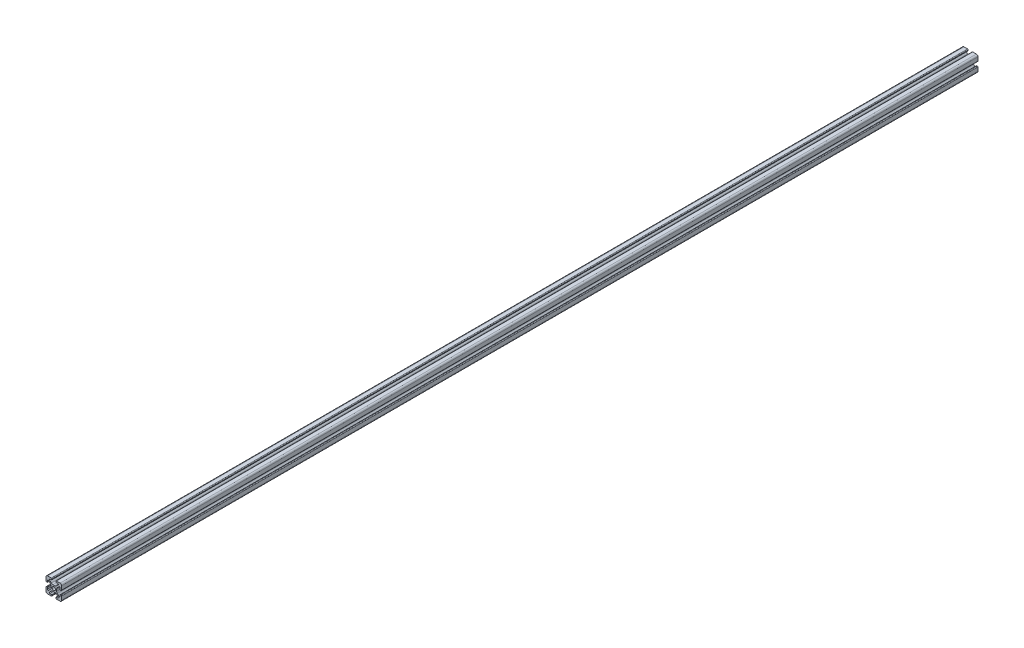
SolidWorks part; units mm, degrees
ref_plane "Front Plane" through (0, 0, 0) normal (0, 0, 1) x (1, 0, 0)
ref_plane "Top Plane" through (0, 0, 0) normal (0, 1, 0) x (1, 0, 0)
ref_plane "Right Plane" through (0, 0, 0) normal (1, 0, 0) x (0, 0, -1)
sketch "Sketch1" plane through (0, 0, 0) normal (0, 0, 1) x (1, 0, 0)
  line L2 (-9.9949, 7.9883) -> (-9.9949, 3.2893)
  line L3 (-7.9883, 9.9949) -> (-3.2893, 9.9949)
  line L4 (-2.5019, 9.2075) -> (-2.5019, 8.4963)
  line L5 (-2.8067, 8.1915) -> (-4.9149, 8.1915)
  line L6 (-5.5076, 6.7606) -> (-3.2528, 4.5058)
  line L7 (-6.7606, 5.5076) -> (-4.5058, 3.2528)
  line L8 (-8.1915, 4.9149) -> (-8.1915, 2.8067)
  line L9 (-8.4963, 2.5019) -> (-9.2075, 2.5019)
  line L11 (-1.1334, 3.6279) -> (1.1334, 3.6279)
  line L12 (-3.6279, 1.1334) -> (-3.6279, -1.1334)
  line L13 (8.4963, 2.5019) -> (9.2075, 2.5019)
  line L14 (8.1915, 4.9149) -> (8.1915, 2.8067)
  line L15 (9.9949, 7.9883) -> (9.9949, 3.2893)
  line L16 (7.9883, 9.9949) -> (3.2893, 9.9949)
  line L17 (2.5019, 9.2075) -> (2.5019, 8.4963)
  line L18 (2.8067, 8.1915) -> (4.9149, 8.1915)
  line L19 (3.6279, 1.1334) -> (3.6279, -1.1334)
  line L20 (5.5076, 6.7606) -> (3.2528, 4.5058)
  line L21 (6.7606, 5.5076) -> (4.5058, 3.2528)
  line L22 (-8.4963, -2.5019) -> (-9.2075, -2.5019)
  line L23 (-8.1915, -4.9149) -> (-8.1915, -2.8067)
  line L24 (-6.7606, -5.5076) -> (-4.5058, -3.2528)
  line L25 (-5.5076, -6.7606) -> (-3.2528, -4.5058)
  line L26 (-2.8067, -8.1915) -> (-4.9149, -8.1915)
  line L27 (-2.5019, -9.2075) -> (-2.5019, -8.4963)
  line L28 (-7.9883, -9.9949) -> (-3.2893, -9.9949)
  line L29 (-9.9949, -7.9883) -> (-9.9949, -3.2893)
  line L30 (9.9949, -7.9883) -> (9.9949, -3.2893)
  line L31 (7.9883, -9.9949) -> (3.2893, -9.9949)
  line L32 (2.5019, -9.2075) -> (2.5019, -8.4963)
  line L33 (2.8067, -8.1915) -> (4.9149, -8.1915)
  line L34 (5.5076, -6.7606) -> (3.2528, -4.5058)
  line L35 (6.7606, -5.5076) -> (4.5058, -3.2528)
  line L36 (8.1915, -4.9149) -> (8.1915, -2.8067)
  line L37 (8.4963, -2.5019) -> (9.2075, -2.5019)
  line L38 (-1.1334, -3.6279) -> (1.1334, -3.6279)
  circle A0 centre (0, 0) radius 2.1463
  arc A1 (-9.9949, 7.9883) -> (-7.9883, 9.9949) centre (-7.9883, 7.9883) cw
  arc A2 (-6.7606, 5.5076) -> (-8.1915, 4.9149) centre (-7.3533, 4.9149) ccw
  arc A3 (-4.9149, 8.1915) -> (-5.5076, 6.7606) centre (-4.9149, 7.3533) ccw
  arc A4 (-3.2893, 9.9949) -> (-2.5019, 9.2075) centre (-3.2893, 9.2075) cw
  arc A5 (-9.9949, 3.2893) -> (-9.2075, 2.5019) centre (-9.2075, 3.2893) ccw
  arc A6 (-8.1915, 2.8067) -> (-8.4963, 2.5019) centre (-8.4963, 2.8067) cw
  arc A7 (-2.5019, 8.4963) -> (-2.8067, 8.1915) centre (-2.8067, 8.4963) cw
  arc A8 (-1.1334, 3.6279) -> (-3.2528, 4.5058) centre (-1.1334, 6.6251) cw
  arc A9 (-3.6279, 1.1334) -> (-4.5058, 3.2528) centre (-6.6251, 1.1334) ccw
  arc A10 (8.1915, 2.8067) -> (8.4963, 2.5019) centre (8.4963, 2.8067) ccw
  arc A11 (9.9949, 3.2893) -> (9.2075, 2.5019) centre (9.2075, 3.2893) cw
  arc A12 (9.9949, 7.9883) -> (7.9883, 9.9949) centre (7.9883, 7.9883) ccw
  arc A13 (3.2893, 9.9949) -> (2.5019, 9.2075) centre (3.2893, 9.2075) ccw
  arc A14 (2.5019, 8.4963) -> (2.8067, 8.1915) centre (2.8067, 8.4963) ccw
  arc A15 (1.1334, 3.6279) -> (3.2528, 4.5058) centre (1.1334, 6.6251) ccw
  arc A16 (3.6279, 1.1334) -> (4.5058, 3.2528) centre (6.6251, 1.1334) cw
  arc A17 (6.7606, 5.5076) -> (8.1915, 4.9149) centre (7.3533, 4.9149) cw
  arc A18 (4.9149, 8.1915) -> (5.5076, 6.7606) centre (4.9149, 7.3533) cw
  arc A19 (-3.6279, -1.1334) -> (-4.5058, -3.2528) centre (-6.6251, -1.1334) cw
  arc A20 (-1.1334, -3.6279) -> (-3.2528, -4.5058) centre (-1.1334, -6.6251) ccw
  arc A21 (-2.5019, -8.4963) -> (-2.8067, -8.1915) centre (-2.8067, -8.4963) ccw
  arc A22 (-8.1915, -2.8067) -> (-8.4963, -2.5019) centre (-8.4963, -2.8067) ccw
  arc A23 (-9.9949, -3.2893) -> (-9.2075, -2.5019) centre (-9.2075, -3.2893) cw
  arc A24 (-3.2893, -9.9949) -> (-2.5019, -9.2075) centre (-3.2893, -9.2075) ccw
  arc A25 (-4.9149, -8.1915) -> (-5.5076, -6.7606) centre (-4.9149, -7.3533) cw
  arc A26 (-6.7606, -5.5076) -> (-8.1915, -4.9149) centre (-7.3533, -4.9149) cw
  arc A27 (-9.9949, -7.9883) -> (-7.9883, -9.9949) centre (-7.9883, -7.9883) ccw
  arc A28 (9.9949, -7.9883) -> (7.9883, -9.9949) centre (7.9883, -7.9883) cw
  arc A29 (6.7606, -5.5076) -> (8.1915, -4.9149) centre (7.3533, -4.9149) ccw
  arc A30 (4.9149, -8.1915) -> (5.5076, -6.7606) centre (4.9149, -7.3533) ccw
  arc A31 (3.2893, -9.9949) -> (2.5019, -9.2075) centre (3.2893, -9.2075) cw
  arc A32 (9.9949, -3.2893) -> (9.2075, -2.5019) centre (9.2075, -3.2893) ccw
  arc A33 (8.1915, -2.8067) -> (8.4963, -2.5019) centre (8.4963, -2.8067) cw
  arc A34 (2.5019, -8.4963) -> (2.8067, -8.1915) centre (2.8067, -8.4963) cw
  arc A35 (1.1334, -3.6279) -> (3.2528, -4.5058) centre (1.1334, -6.6251) cw
  arc A36 (3.6279, -1.1334) -> (4.5058, -3.2528) centre (6.6251, -1.1334) ccw
extrude "Boss-Extrude1" add sketch "Sketch1" along normal mid plane 1170
